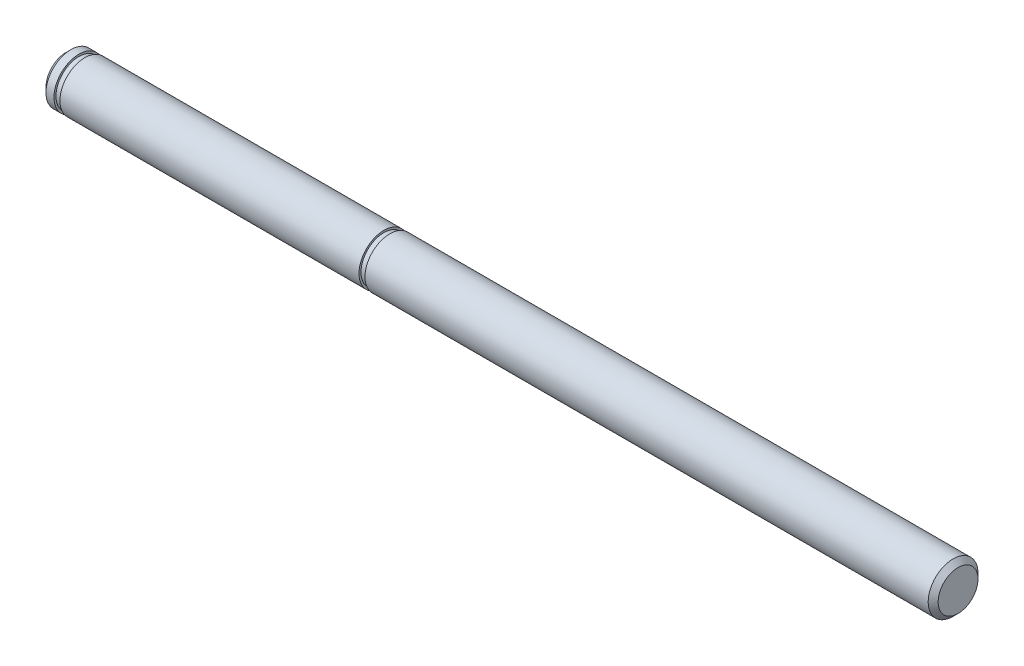
SolidWorks part; units mm, degrees
ref_plane "Front Plane" through (0, 0, 0) normal (0, 0, 1) x (1, 0, 0)
ref_plane "Top Plane" through (0, 0, 0) normal (0, 1, 0) x (1, 0, 0)
ref_plane "Right Plane" through (0, 0, 0) normal (1, 0, 0) x (0, 0, -1)
sketch "Sketch2" plane through (0, 0, 0) normal (1, 0, 0) x (0, 0, -1)
  circle A0 centre (0, 0) radius 3.175
  dimension "D1" = 6.35
extrude "Boss-Extrude1" add sketch "Sketch2" along normal blind 113.665
chamfer "Chamfer1" distance 0.635 angle 45 2 edges at (113.665, 0, -3.175) (0, 0, -3.175)
sketch "Sketch3" plane through (0, 0, 0) normal (0, 0, 1) x (1, 0, 0)
  line L0 (113.03, 3.175) -> (0.635, 3.175) construction
  line L1 (1.651, 2.921) -> (2.413, 2.921)
  line L2 (1.651, 2.921) -> (1.651, 3.175)
  line L3 (1.651, 3.175) -> (2.413, 3.175)
  line L4 (2.413, 2.921) -> (2.413, 3.175)
  line L5 (1.651, 2.921) -> (2.413, 3.175) construction
  line L6 (1.651, 3.175) -> (2.413, 2.921) construction
  line L7 (0, 2.54) -> (0, -2.54) construction
  line L8 (0, 0) -> (113.6303, 0) construction
  line L9 (21.463, 2.921) -> (21.463, 8.4291) construction
  line L10 (41.275, 3.175) -> (40.513, 2.921) construction
  line L11 (41.275, 2.921) -> (40.513, 3.175) construction
  line L12 (40.513, 2.921) -> (40.513, 3.175)
  line L13 (41.275, 2.921) -> (41.275, 3.175)
  line L14 (41.275, 2.921) -> (40.513, 2.921)
  line L15 (41.275, 3.175) -> (40.513, 3.175)
  point P0 (2.032, 3.048)
  point P18 (40.894, 3.048)
  dimension "D1" = 0.762
  dimension "D2" = 1.651
  dimension "D3" = 0.254
  dimension "D4" = 19.05
revolve "Cut-Revolve1" cut sketch "Sketch3" angle 360 about L8
